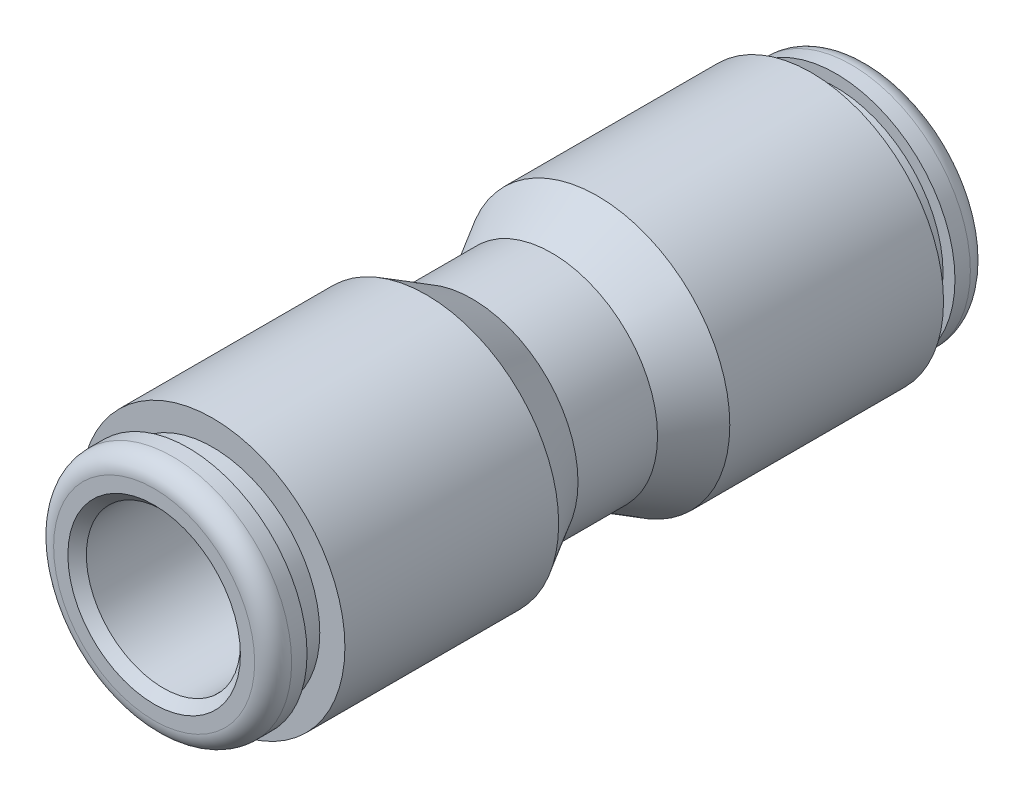
SolidWorks part; units mm, degrees
ref_plane "Front Plane" through (0, 0, 0) normal (0, 0, 1) x (1, 0, 0)
ref_plane "Top Plane" through (0, 0, 0) normal (0, 1, 0) x (1, 0, 0)
ref_plane "Right Plane" through (0, 0, 0) normal (1, 0, 0) x (0, 0, -1)
sketch "Sketch1" plane through (0, 0, 0) normal (1, 0, 0) x (0, 0, -1)
  line L0 (13.353, 4.905) -> (13.988, 4.905)
  line L1 (3.5268, 5.45) -> (12.337, 5.45)
  line L2 (0, 4.36) -> (0, 2.413)
  line L3 (0.25, 3.175) -> (14.369, 3.175)
  line L4 (14.75, 4.143) -> (14.75, 3.556)
  line L5 (0.25, 3.175) -> (0.25, 2.413)
  line L6 (12.337, 5.45) -> (12.337, 4.4145)
  line L7 (12.337, 4.4145) -> (13.353, 4.4145)
  line L8 (13.353, 4.905) -> (13.353, 4.4145)
  line L9 (0.25, 2.413) -> (0, 2.413)
  line L10 (0, 0) -> (14.75, 0) construction
  line L12 (14.369, 3.175) -> (14.75, 3.556)
  line L13 (0, 0) -> (0, 2.413) construction
  line L14 (0, 4.36) -> (1.6389, 4.36)
  line L15 (1.6389, 4.36) -> (3.5268, 5.45)
  arc A0 (13.988, 4.905) -> (14.75, 4.143) centre (13.988, 4.143) cw
  point P1 (14.75, 3.175)
  point P20 (14.75, 4.905)
  dimension "D4" = 0.762
  dimension "tube od" = 6.35
  dimension "D1" = 1.397
  dimension "D2" = 1.016
  dimension "D3" = 8.829
  dimension "D6" = 9.81
  dimension "D9" = 30
  dimension "D10" = 8.72
  dimension "D5" = 13.1111
  dimension "D8" = 0.762
revolve "Revolve1" add sketch "Sketch1" angle 360 about L10
mirror "Mirror1" about plane through (0, 0, 0) normal (0, 0, 1) of "Revolve1"
equation "\"D3@Sketch1\" = \"D6@Sketch1\"*.9"
equation "\"D6@Sketch1\" = \"G@Sketch1\"*.9"
equation "\"D10@Sketch1\" = \"G@Sketch1\"*.8"
equation "\"D5@Sketch1\" = \"L@Sketch1\"/2.25"
